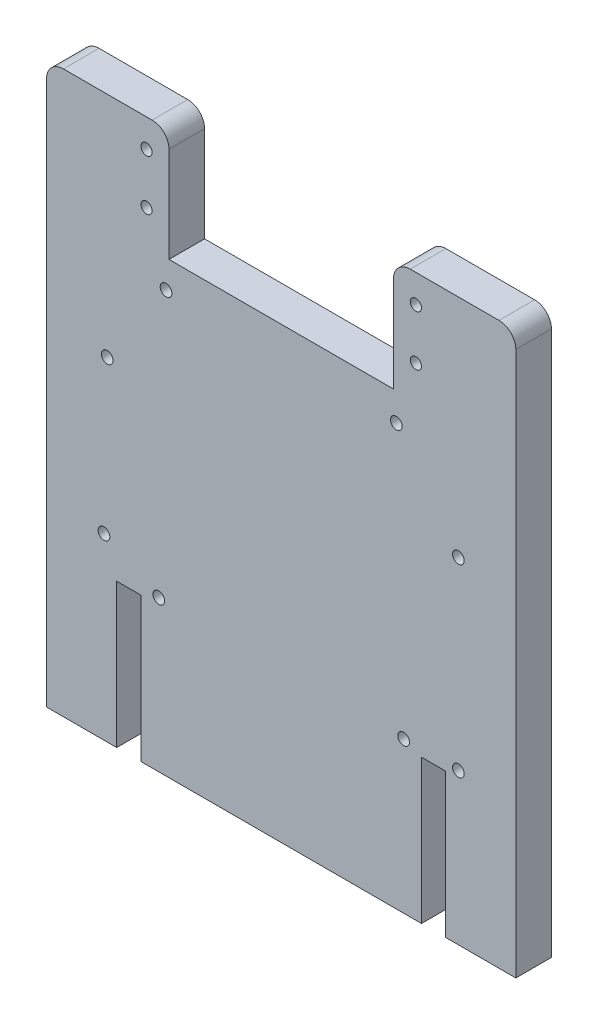
SolidWorks part; units mm, degrees
material "Balsa"
ref_plane "Front Plane" through (0, 0, 0) normal (0, 0, 1) x (1, 0, 0)
ref_plane "Top Plane" through (0, 0, 0) normal (0, 1, 0) x (1, 0, 0)
ref_plane "Right Plane" through (0, 0, 0) normal (1, 0, 0) x (0, 0, -1)
sketch "Sketch1" plane through (0, 0, 0) normal (0, 0, 1) x (1, 0, 0)
  line L0 (0, 0) -> (0, 100)
  line L1 (0, 100) -> (21.818, 100)
  line L2 (21.818, 100) -> (21.818, 80)
  line L3 (21.818, 80) -> (61.818, 80)
  line L4 (61.818, 80) -> (61.818, 100)
  line L5 (61.818, 100) -> (83.636, 100)
  line L6 (83.636, 100) -> (83.636, 0)
  line L7 (16.818, 0) -> (66.818, 0)
  line L8 (12.5, 0) -> (12.5, 25.68)
  line L9 (12.5, 25.68) -> (16.818, 25.68)
  line L10 (16.818, 25.68) -> (16.818, 0)
  line L11 (66.818, 0) -> (66.818, 25.68)
  line L12 (66.818, 25.68) -> (71.136, 25.68)
  line L13 (71.136, 25.68) -> (71.136, 0)
  line L14 (12.5, 0) -> (0, 0)
  line L15 (71.136, 0) -> (83.636, 0)
  dimension "D1" = 50
  dimension "D2" = 100
  dimension "D3" = 40
  dimension "D4" = 20
  dimension "D5" = 4.318
  dimension "D6" = 25.68
  dimension "D7" = 12.5
extrude "main shape" add sketch "Sketch1" along normal blind 6.35
fillet "Fillet1" radius 3 4 edges at (83.636, 100, 3.175) (61.818, 100, 3.175) (21.818, 100, 3.175) (0, 100, 3.175)
sketch "locations for shoulder servo mount" plane through (0, 0, 6.35) normal (0, 0, 1) x (1, 0, 0)
  line L0 (17.818, 90.5) -> (0, 90.5) construction
  line L1 (17.818, 95) -> (65.818, 95) construction
  line L2 (17.818, 95) -> (17.818, 86) construction
  line L3 (17.818, 86) -> (65.818, 86) construction
  line L4 (65.818, 95) -> (65.818, 86) construction
  line L5 (0, 97) -> (0, 0) construction
  line L6 (65.818, 90.5) -> (83.636, 90.5) construction
  line L7 (83.636, 0) -> (83.636, 97) construction
  line L8 (18.818, 100) -> (3, 100) construction
  dimension "D1" = 48
  dimension "D2" = 9
  dimension "D3" = 5
hole_wizard "#3-48 Tapped Hole1" positions "Sketch4" profile "Sketch3" tap size "#3-48" standard "Ansi Inch"
sketch "Sketch4" plane through (0, 0, 6.35) normal (0, 0, 1) x (1, 0, 0)
  point P1 (17.818, 95)
  point P4 (17.818, 86)
  point P7 (65.818, 86)
  point P10 (65.818, 95)
sketch "Sketch3" plane through (17.818, 95, 6.35) normal (1, 0, 0) x (0, -1, 0)
  line L0 (0, 0) -> (0, 7.209)
  line L1 (0, 7.209) -> (0.9969, 6.61)
  line L2 (0.9969, 6.61) -> (0.9969, 0)
  line L5 (0.9969, 0) -> (0, 0)
  line L10 (0, 7.209) -> (-0.997, 6.61) construction
  line L11 (0, -6.35) -> (0, 107.95) construction
  dimension "Tap Drill Dia." = 1.9939
  dimension "Tap Drill Depth" = 6.61
  dimension "Drill Angle" = 118
cosmetic thread "Hole Thread1" parameters "D1"=5.03, "D2"=2.5146
cosmetic thread "Hole Thread2" parameters "D1"=5.03, "D2"=2.5146
cosmetic thread "Hole Thread3" parameters "D1"=5.03, "D2"=2.5146
cosmetic thread "Hole Thread4" parameters "D1"=5.03, "D2"=2.5146
sketch "arduino mount holes" plane through (0, 0, 0) normal (0, 0, 1) x (1, 0, 0)
  line L0 (61.818, 80) -> (21.818, 80) construction
  line L1 (20, 45.438) -> (21.3, 45.438) construction
  line L2 (20, 45.438) -> (20, 26.9) construction
  line L3 (20, 26.9) -> (73.4, 26.9) construction
  line L4 (73.4, 59.8) -> (73.4, 26.9) construction
  line L5 (0, 97) -> (0, 0) construction
  line L6 (21.3, 45.438) -> (21.3, 75) construction
  line L7 (21.3, 75) -> (73.4, 75) construction
  line L8 (73.4, 59.8) -> (73.4, 75) construction
  line L9 (63.636, 26.9) -> (63.636, 31.9) construction
  line L10 (63.636, 31.9) -> (62.336, 31.9) construction
  line L11 (62.336, 31.9) -> (62.336, 75) construction
  line L12 (62.336, 75) -> (10.236, 75) construction
  line L13 (10.236, 75) -> (10.236, 31.9) construction
  line L14 (10.236, 31.9) -> (10.236, 26.9) construction
  line L15 (10.236, 26.9) -> (63.636, 26.9) construction
  line L16 (83.636, 0) -> (83.636, 97) construction
  point P20 (10.236, 59.8)
  point P21 (73.4, 31.9)
  dimension "D1" = 52.1
  dimension "D2" = 15.2
  dimension "D3" = 1.3
  dimension "D4" = 15.2
  dimension "D5" = 5
  dimension "D6" = 20
  dimension "D7" = 20
  dimension "D8" = 52.1
  dimension "D9" = 5
  dimension "D10" = 27.9
  dimension "D11" = 5
hole_wizard "#3-48 Tapped Hole1 for arduino mount" positions "Sketch7" profile "Sketch6" tap size "#3-56" standard "Ansi Inch"
sketch "Sketch7" plane through (0, 0, 6.35) normal (0, 0, 1) x (1, 0, 0)
  point P1 (21.3, 75)
  point P4 (20, 26.9)
  point P7 (73.4, 26.9)
  point P10 (73.4, 59.8)
  point P18 (10.236, 31.9)
  point P24 (63.636, 26.9)
  point P34 (62.336, 75)
  point P41 (10.8117, 59.3939)
sketch "Sketch6" plane through (21.3, 75, 6.35) normal (1, 0, 0) x (0, -1, 0)
  line L0 (0, 0) -> (0, 7.9257)
  line L1 (0, 7.9257) -> (1.0414, 7.3)
  line L2 (1.0414, 7.3) -> (1.0414, 0)
  line L5 (1.0414, 0) -> (0, 0)
  line L10 (0, 7.9257) -> (-1.0414, 7.3) construction
  line L11 (0, -6.35) -> (0, 107.95) construction
  dimension "Tap Drill Dia." = 2.0828
  dimension "Tap Drill Depth" = 7.3
  dimension "Drill Angle" = 118
cosmetic thread "Hole Thread5" parameters "D1"=5.03, "D2"=2.5146
cosmetic thread "Hole Thread6" parameters "D1"=5.03, "D2"=2.5146
cosmetic thread "Hole Thread7" parameters "D1"=5.03, "D2"=2.5146
cosmetic thread "Hole Thread8" parameters "D1"=5.03, "D2"=2.5146
cosmetic thread "Hole Thread9" parameters "D1"=5.03, "D2"=2.5146
cosmetic thread "Hole Thread10" parameters "D1"=5.03, "D2"=2.5146
cosmetic thread "Hole Thread12" parameters "D1"=5.03, "D2"=2.5146
cosmetic thread "Hole Thread13" parameters "D1"=5.03, "D2"=2.5146
